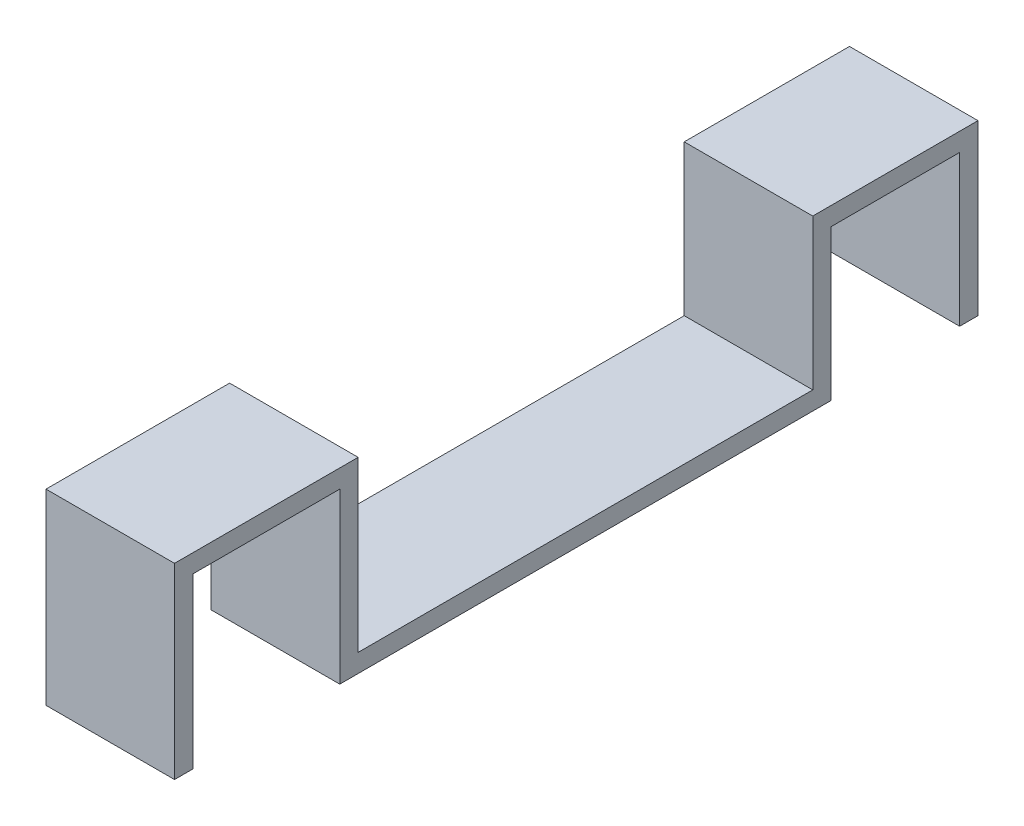
SolidWorks part; units mm, degrees
ref_plane "前基準面" through (0, 0, 0) normal (0, 0, 1) x (1, 0, 0)
ref_plane "上基準面" through (0, 0, 0) normal (0, 1, 0) x (1, 0, 0)
ref_plane "右基準面" through (0, 0, 0) normal (1, 0, 0) x (0, 0, -1)
sketch "草圖1" plane through (0, 0, 0) normal (0, 1, 0) x (1, 0, 0)
  line L1 (-17.5, -61.9) -> (17.5, -61.9)
  line L2 (-17.5, -61.9) -> (-17.5, 61.9)
  line L3 (-17.5, 61.9) -> (17.5, 61.9)
  line L4 (17.5, -61.9) -> (17.5, 61.9)
  line L5 (0, 61.9) -> (0, -61.9) construction
  line L6 (-17.5, 0) -> (17.5, 0) construction
  point P0 (0, 0)
  point P4 (17.5, -61.9)
  dimension "D1" = 123.8
  dimension "D2" = 35
extrude "填料-伸長1" add sketch "草圖1" along normal blind 5 contours L2 L3 L4 L1
sketch "草圖2" plane through (0, 0, -61.9) normal (0, 0, -1) x (-1, 0, 0)
  line L0 (-17.5, 0) -> (-17.5, 5)
  line L1 (-17.5, 0) -> (17.5, 0)
  line L2 (-17.5, 5) -> (17.5, 5)
  line L3 (17.5, 0) -> (17.5, 5)
  line L4 (0, 0) -> (0, 5) construction
  line L5 (-17.5, 2.5) -> (17.5, 2.5) construction
  line L6 (-17.5, 0) -> (17.5, 0)
  line L8 (-17.5, 0) -> (-17.5, 5)
  line L9 (-17.5, 5) -> (17.5, 5)
  line L10 (17.5, 0) -> (17.5, 5)
  line L11 (0, 5) -> (0, -12.0296) construction
  line L12 (-17.5, 2.5) -> (17.5, 2.5) construction
  line L13 (-17.5, 0) -> (17.5, 0)
  line L14 (-17.5, 0) -> (-17.5, 46)
  line L15 (-17.5, 46) -> (17.5, 46)
  line L16 (17.5, 46) -> (17.5, 0)
  point P0 (-17.5, 5)
  point P1 (-17.5, 0)
  point P3 (-17.5, 5)
  point P5 (17.5, 5)
  point P16 (0, 2.5)
  point P18 (0, 0)
  point P22 (0, 0)
  point P23 (0, 0)
  point P24 (0, 0)
  line M11 (17.5, 5) -> (-17.5, 5)
  dimension "D1" = 46
extrude "填料-伸長3" add sketch "草圖2" along normal blind 5 separate body contours L16 L15 L14 M11
sketch "草圖3" plane through (0, 0, -61.9) normal (0, 0, -1) x (-1, 0, 0)
  line L1 (-17.5, 5) -> (17.5, 5)
  line L2 (-17.5, 5) -> (-17.5, 0)
  line L3 (-17.5, 0) -> (17.5, 0)
  line L4 (17.5, 5) -> (17.5, 0)
extrude "填料-伸長4" add sketch "草圖3" along normal blind 5
sketch "草圖4" plane through (0, 0, -66.9) normal (0, 0, -1) x (-1, 0, 0)
  line L0 (-17.5, 46) -> (-17.5, 41)
  line L1 (-17.5, 46) -> (-17.5, 0) construction
  line L2 (-17.5, 41) -> (17.5, 41)
  line L3 (17.5, 0) -> (17.5, 46) construction
  line L4 (17.5, 41) -> (17.5, 46)
  line L5 (17.5, 46) -> (-17.5, 46)
  dimension "D1" = 5
extrude "填料-伸長5" add sketch "草圖4" along normal blind 40
sketch "草圖5" plane through (0, 41, 0) normal (0, -1, 0) x (1, 0, 0)
  line L0 (-17.5, -106.9) -> (-17.5, -101.9)
  line L1 (-17.5, -106.9) -> (-17.5, -66.9) construction
  line L2 (-17.5, -101.9) -> (17.5, -101.9)
  line L3 (17.5, -106.9) -> (17.5, -66.9) construction
  line L4 (17.5, -101.9) -> (17.5, -106.9)
  line L5 (17.5, -106.9) -> (-17.5, -106.9)
  point P5 (0, 0)
  dimension "D1" = 5
extrude "填料-伸長6" add sketch "草圖5" along normal blind 41 contours L5 L0 L2 L4
sketch "草圖8" plane through (0, 0, 61.9) normal (0, 0, 1) x (1, 0, 0)
  line L0 (-17.5, 2.5) -> (17.5, 2.5) construction
  line L1 (-17.5, 5) -> (-17.5, 0) construction
  line L2 (17.5, 5) -> (17.5, 0) construction
  line L4 (-17.5, 0) -> (17.5, 0)
  line L5 (-17.5, 0) -> (-17.5, 5)
  line L6 (-17.5, 5) -> (17.5, 5)
  line L7 (17.5, 0) -> (17.5, 5)
extrude "填料-伸長7" add sketch "草圖8" along normal blind 5
sketch "草圖12" plane through (0, 5, 0) normal (0, 1, 0) x (1, 0, 0)
  line L0 (-17.5, -66.9) -> (-17.5, -61.9)
  line L1 (-17.5, -66.9) -> (-17.5, 61.9) construction
  line L2 (-17.5, -61.9) -> (17.5, -61.9)
  line L3 (17.5, -66.9) -> (17.5, 61.9) construction
  line L4 (17.5, -61.9) -> (17.5, -66.9)
  line L5 (17.5, -66.9) -> (-17.5, -66.9) construction
  line L6 (17.5, -66.9) -> (-17.5, -66.9)
  dimension "D1" = 5
extrude "填料-伸長8" add sketch "草圖12" along normal blind 46
sketch "草圖13" plane through (0, 0, 66.9) normal (0, 0, 1) x (1, 0, 0)
  line L0 (-17.5, 51) -> (-17.5, 46)
  line L1 (-17.5, 46) -> (17.5, 46)
  line L2 (17.5, 0) -> (17.5, 51) construction
  line L3 (17.5, 46) -> (17.5, 51)
  line L4 (-17.5, 51) -> (17.5, 51) construction
  line L5 (17.5, 51) -> (-17.5, 51)
extrude "填料-伸長9" add sketch "草圖13" along normal blind 45
sketch "草圖14" plane through (0, 46, 0) normal (0, -1, 0) x (1, 0, 0)
  line L0 (17.5, 111.9) -> (17.5, 66.9) construction
  line L1 (-17.5, 111.9) -> (17.5, 111.9)
  line L2 (-17.5, 111.9) -> (-17.5, 106.9)
  line L3 (-17.5, 106.9) -> (17.5, 106.9)
  line L4 (17.5, 111.9) -> (17.5, 106.9)
  dimension "D1" = 5
extrude "填料-伸長10" add sketch "草圖14" along normal blind 46
